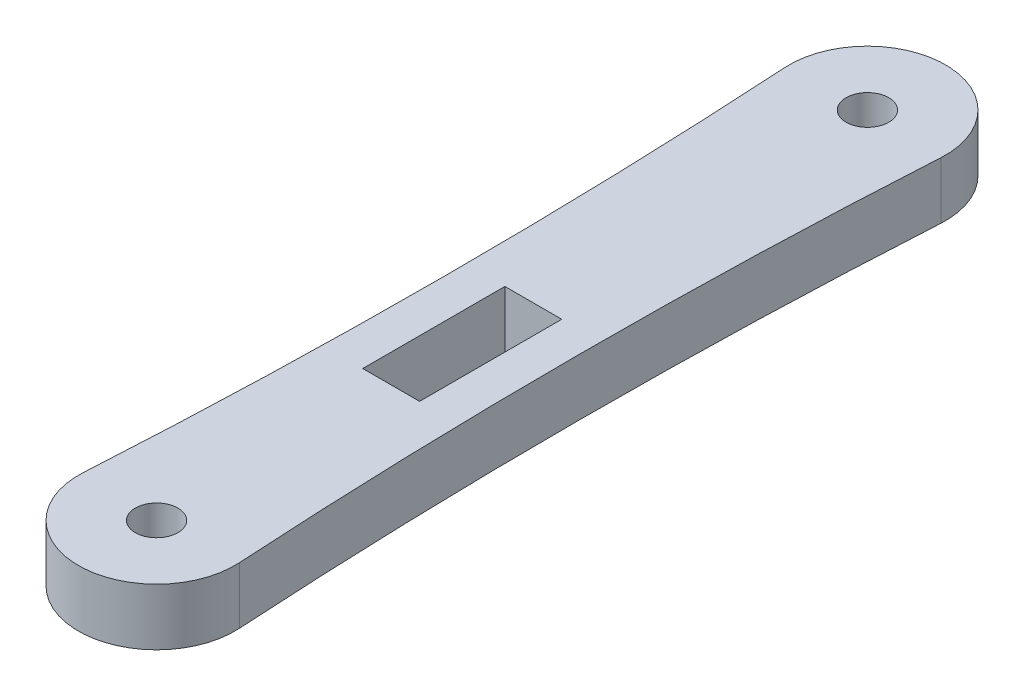
SolidWorks part; units mm, degrees
ref_plane "Front Plane" through (0, 0, 0) normal (0, 0, 1) x (1, 0, 0)
ref_plane "Top Plane" through (0, 0, 0) normal (0, 1, 0) x (1, 0, 0)
ref_plane "Right Plane" through (0, 0, 0) normal (1, 0, 0) x (0, 0, -1)
sketch "Sketch1" plane through (0, 0, 0) normal (0, 1, 0) x (1, 0, 0)
  line L0 (0, 0) -> (0, 50) construction
  line L3 (-4.75, 25) -> (4.75, 25) construction
  line L5 (-2, 26.5) -> (2, 26.5)
  line L6 (-2, 26.5) -> (-2, 16.5)
  line L7 (-2, 16.5) -> (2, 16.5)
  line L8 (2, 26.5) -> (2, 16.5)
  circle A2 centre (0, 0) radius 1.5
  circle A3 centre (0, 50) radius 1.5
  arc A8 (-5.4901, 0.3297) -> (5.4901, 0.3297) centre (0, 0) ccw
  arc A9 (5.4901, 49.6703) -> (-5.4901, 49.6703) centre (0, 50) ccw
  arc A10 (-5.4901, 49.6703) -> (-5.4901, 0.3297) centre (-416.2917, 25) cw
  arc A11 (5.4901, 49.6703) -> (5.4901, 0.3297) centre (416.2917, 25) ccw
  circle A12 centre (0, 25) radius 1.5 construction
  point P3 (0, 25)
  point P16 (-4.75, 25)
  point P19 (4.75, 25)
  point P23 (0, 25)
  point P25 (0, 16.5)
  dimension "D1" = 3
  dimension "D2" = 50
  dimension "D3" = 4
  dimension "D5" = 3
  dimension "D4" = 9.5
  dimension "D6" = 4
  dimension "D7" = 10
extrude "Boss-Extrude1" add sketch "Sketch1" along normal blind 4
